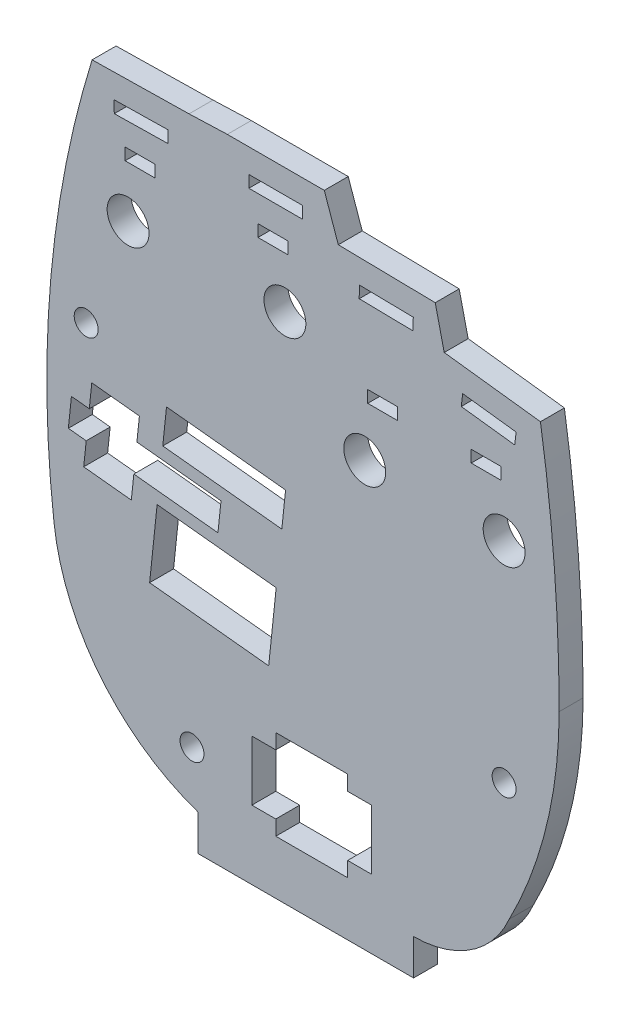
SolidWorks part; units mm, degrees
ref_plane "Front Plane" through (0, 0, 0) normal (0, 0, 1) x (1, 0, 0)
ref_plane "Top Plane" through (0, 0, 0) normal (0, 1, 0) x (1, 0, 0)
ref_plane "Right Plane" through (0, 0, 0) normal (1, 0, 0) x (0, 0, -1)
sketch "Sketch1" plane through (0, 0, 0) normal (0, 0, 1) x (1, 0, 0)
  line L0 (-4.5, 78.51) -> (-4.5, 76.51)
  line L1 (4.5, 78.51) -> (-4.5, 78.51)
  line L2 (-4.5, 76.51) -> (4.5, 76.51)
  line L3 (4.5, 76.51) -> (4.5, 78.51)
  line L4 (-4, -2.5) -> (0, -2.5)
  line L5 (0, 0) -> (18.54, 0) construction
  line L6 (0, 0) -> (0, 82.51) construction
  line L7 (12, 0) -> (0, 0)
  line L8 (0, 0) -> (-22.59, 0) construction
  line L9 (32.6473, 57.3216) -> (37.6473, 57.3216)
  line L10 (-12.9786, -18) -> (-12.9786, -24)
  line L11 (32.6473, 55.3216) -> (37.6473, 55.3216)
  line L12 (37.6473, 55.3216) -> (37.6473, 57.3216)
  line L13 (32.6473, 57.3216) -> (32.6473, 55.3216)
  line L14 (-27.02, 78.0626) -> (-18.0213, 78.2186)
  line L15 (-27.02, 78.0626) -> (-26.9853, 76.0629)
  line L16 (-26.9853, 76.0629) -> (-17.9866, 76.2189)
  line L17 (-17.9866, 76.2189) -> (-18.0213, 78.2186)
  line L18 (15.3631, 57.3216) -> (20.3631, 57.3216)
  line L19 (15.3631, 55.3216) -> (20.3631, 55.3216)
  line L20 (20.3631, 55.3216) -> (20.3631, 57.3216)
  line L21 (15.3631, 57.3216) -> (15.3631, 55.3216)
  line L22 (-2.9786, 72.1512) -> (2.0214, 72.1512)
  line L23 (13.9708, 71.7441) -> (13.9359, 69.7445)
  line L24 (13.9359, 69.7445) -> (22.9346, 69.5874)
  line L25 (-2.9786, 70.1512) -> (2.0214, 70.1512)
  line L26 (22.9695, 71.5871) -> (13.9708, 71.7441)
  line L27 (22.9346, 69.5874) -> (22.9695, 71.5871)
  line L28 (-22.59, 0) -> (-22.59, 82.14) construction
  line L29 (2.0214, 70.1512) -> (2.0214, 72.1512)
  line L30 (28.1404, 69.0671) -> (44.2196, 67.0929)
  line L31 (-2.9786, 72.1512) -> (-2.9786, 70.1512)
  line L32 (40.159, 63.5614) -> (31.226, 64.6582)
  line L33 (1.6326, 35.9121) -> (1.0057, 29.9449)
  line L34 (31.226, 64.6582) -> (30.9823, 62.6731)
  line L35 (-25.179, 72.1512) -> (-20.179, 72.1512)
  line L36 (18.54, 0) -> (18.54, 75.665) construction
  line L37 (0, 0) -> (36.18, 0) construction
  line L38 (-25.179, 70.1512) -> (-20.179, 70.1512)
  line L39 (30.9823, 62.6731) -> (39.9153, 61.5763)
  line L40 (-20.179, 70.1512) -> (-20.179, 72.1512)
  line L41 (-25.179, 72.1512) -> (-25.179, 70.1512)
  line L42 (39.9153, 61.5763) -> (40.159, 63.5614)
  line L43 (1.6326, 35.9121) -> (-18.2579, 38.0017)
  line L44 (0.0654, 20.9942) -> (-1.1883, 9.0599)
  line L45 (12, 0) -> (12, -2.5)
  line L46 (-18.8848, 32.0346) -> (1.0057, 29.9449)
  line L47 (12, -15) -> (0, -15)
  line L48 (-9.666, 24.0728) -> (-9.153, 28.9559)
  line L49 (-34.657, 26.6982) -> (-34.144, 31.5814)
  line L50 (-9.153, 28.9559) -> (-23.2057, 30.4322)
  line L51 (-32.0928, 22.4068) -> (-31.6749, 26.385)
  line L52 (-34.657, 26.6982) -> (-31.6749, 26.385)
  line L53 (-23.7187, 25.5491) -> (-9.666, 24.0728)
  line L54 (-23.2057, 30.4322) -> (-22.7877, 34.4103)
  line L55 (-24.1366, 21.571) -> (-32.0928, 22.4068)
  line L56 (-18.8848, 32.0346) -> (-18.2579, 38.0017)
  line L57 (-30.744, 35.2462) -> (-31.1619, 31.2681)
  line L58 (-22.7877, 34.4103) -> (-30.744, 35.2462)
  line L59 (-31.1619, 31.2681) -> (-34.144, 31.5814)
  line L60 (-24.1366, 21.571) -> (-23.7187, 25.5491)
  line L61 (-19.8251, 23.0838) -> (0.0654, 20.9942)
  line L62 (-21.0789, 11.1495) -> (-1.1883, 9.0599)
  line L63 (0, -15) -> (0, -12.5)
  line L64 (-4, -12.5) -> (-4, -2.5)
  line L65 (-19.8251, 23.0838) -> (-21.0789, 11.1495)
  line L66 (-12.9786, -24) -> (23.0214, -24)
  line L67 (-4, -12.5) -> (0, -12.5)
  line L68 (0, -2.5) -> (0, 0)
  line L69 (16, -12.5) -> (12, -12.5)
  line L70 (16, -12.5) -> (16, -2.5)
  line L71 (16, -2.5) -> (12, -2.5)
  line L72 (12, -12.5) -> (12, -15)
  line L73 (23.0214, -24) -> (23.0214, -18)
  line L74 (36.18, 0) -> (36.18, 68.08) construction
  line L75 (10.4412, 75.8064) -> (26.6388, 75.5236)
  line L76 (-8.1, 82.51) -> (8.1, 82.51)
  line L77 (-14.4912, 82.2805) -> (-30.6888, 81.9995)
  line L78 (28.1404, 69.0671) -> (26.6388, 75.5236)
  line L79 (-9.4095, 26.5144) -> (4.399, 25.0637) construction
  line L80 (39, -7.5) -> (16, -7.5) construction
  line L81 (10.4412, 75.8064) -> (8.1, 82.51)
  line L82 (-8.1, 82.51) -> (-14.4912, 82.2805)
  line L83 (-34.657, 26.6982) -> (47.343, 26.6982) construction
  line L84 (35.6925, 64.1098) -> (36.18, 68.08) construction
  line L85 (38.1473, 11.8216) -> (-37.0527, 11.8216) construction
  line L86 (-18.8848, 32.0346) -> (-19.8251, 23.0838) construction
  line L87 (-19.355, 27.5592) -> (-38.241, 29.5433) construction
  line L88 (18.4702, 71.6656) -> (18.54, 75.665) construction
  line L89 (-22.5206, 78.1406) -> (-22.59, 82.14) construction
  line L90 (0, 78.51) -> (0, 82.51) construction
  line L91 (38.1473, 46.8216) -> (38.1473, 11.8216) construction
  arc A0 (23.0214, -18) -> (39, -7.5) centre (23.0214, -0.592) ccw
  circle A1 centre (38.1473, 11.8216) radius 2
  arc A2 (-37.0527, 11.8216) -> (-30.6888, 81.9995) centre (130.7995, 31.9779) cw
  circle A3 centre (-24.679, 61.6512) radius 3.5
  circle A4 centre (1.5214, 61.6512) radius 3.5
  circle A5 centre (14.8631, 46.8216) radius 3.5
  circle A6 centre (38.1473, 46.8216) radius 3.5
  arc A7 (-37.0527, 11.8216) -> (-12.9786, -18) centre (-1.2138, 16.1253) ccw
  circle A8 centre (-31.6815, 43.4564) radius 2
  circle A9 centre (-14, -9.1244) radius 2
  arc A10 (47.343, 26.6982) -> (39, -7.5) centre (-26.9181, 26.6982) cw
  arc A11 (47.343, 26.6982) -> (44.2196, 67.0929) centre (-215.4276, 26.6982) ccw
  dimension "D1" = 7
  dimension "D2" = 4
  dimension "D10" = 1.0057
  dimension "D11" = 1.5214
  dimension "D22" = 14.8631
  dimension "D28" = 23.0214
  dimension "D35" = 38.1473
  dimension "D40" = 9.153
  dimension "D41" = 9.666
  dimension "D42" = 12.9786
  dimension "D43" = 14
  dimension "D50" = 24.679
  dimension "D52" = 31.6815
  dimension "D60" = 43.4564
  dimension "D61" = 46.8216
  dimension "D65" = 61.6512
  dimension "D72" = 9.1244
  dimension "D13" = 82.51
  dimension "D15" = 22.59
  dimension "D16" = 82.14
  dimension "D17" = 18.54
  dimension "D20" = 36.18
  dimension "D26" = 16.2
  dimension "D27" = 5
  dimension "D29" = 55.3216
  dimension "D30" = 32.6473
  dimension "D32" = 15.3631
  dimension "D33" = 70.1512
  dimension "D36" = 2.9786
  dimension "D39" = 25.179
  dimension "D53" = 9.0001
  dimension "D46" = 4
  dimension "D48" = 4
  dimension "D19" = 75.665
  dimension "D62" = 2
  dimension "D59" = 21.571
  dimension "D21" = 18
  dimension "D23" = 68.08
  dimension "D37" = 4
  dimension "D47" = 57.3216
  dimension "D57" = 72.1512
  dimension "D45" = 20
  dimension "D49" = 4.5
  dimension "D51" = 25.1285
  dimension "D54" = 8
  dimension "D56" = 14.13
  dimension "D9" = 9
  dimension "D12" = 6
  dimension "D38" = 4.91
  dimension "D8" = 12
  dimension "D14" = 10
  dimension "D18" = 2.5
  dimension "D24" = 4
  dimension "ThumbLinkLengthMCP" = 18.99
  dimension "D25" = 4
  dimension "D34" = 8.1
  dimension "D44" = 35
extrude "Boss-Extrude1" add sketch "Sketch1" along normal blind 4
equation "\"D13@Sketch1\"= \"HL@parametersSketch@prostheticParameters.SLDPRT\" * 0.446'Middle Base Frame"
equation "\"D15@Sketch1\"= \"HB@parametersSketch@prostheticParameters.SLDPRT\" * 0.251'Index Base Frame X"
equation "\"D16@Sketch1\"= \"HL@parametersSketch@prostheticParameters.SLDPRT\" * 0.444'Index Base Frame Y"
equation "\"D17@Sketch1\"= \"HB@parametersSketch@prostheticParameters.SLDPRT\" * 0.206'Ring Base Frame X"
equation "\"D19@Sketch1\"= \"HL@parametersSketch@prostheticParameters.SLDPRT\" * 0.409'Ring base Frame Y"
equation "\"D20@Sketch1\"= \"HB@parametersSketch@prostheticParameters.SLDPRT\" * 0.402'Pinky Base Frame X"
equation "\"D23@Sketch1\"= \"HL@parametersSketch@prostheticParameters.SLDPRT\" * 0.368'Pinky Base Frame Y"
equation "\"D26@Sketch1\"= \"fingerWidth@parametersSketch@prostheticParameters.SLDPRT\"'Fingers Width"
equation "\"D59@Sketch1\"= \"HL@parametersSketch@prostheticParameters.SLDPRT\" * 0.1166'Hole Thumb Y"
equation "\"D40@Sketch1\"= \"HB@parametersSketch@prostheticParameters.SLDPRT\" * 0.1017'Hole Thumb X1"
equation "\"D41@Sketch1\"= \"HB@parametersSketch@prostheticParameters.SLDPRT\" * 0.1074'Hole Thumb X2"
equation "\"ThumbLinkLengthMCP@Sketch1\"= \"HB@parametersSketch@prostheticParameters.SLDPRT\" * 0.211"
equation "\"D53@Sketch1\"= \"fingerWidth@parametersSketch@prostheticParameters.SLDPRT\" * 0.55556"
equation "\"D34@Sketch1\"= \"fingerWidth@parametersSketch@prostheticParameters.SLDPRT\" / 2"
